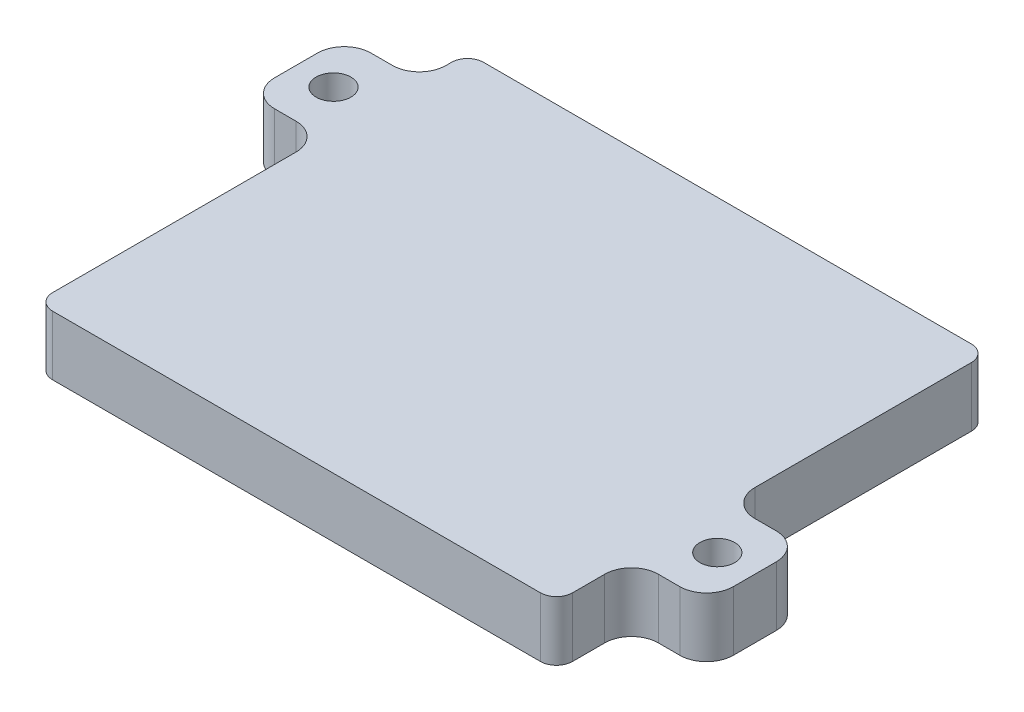
SolidWorks part; units mm, degrees
ref_plane "Front Plane" through (0, 0, 0) normal (0, 0, 1) x (1, 0, 0)
ref_plane "Top Plane" through (0, 0, 0) normal (0, 1, 0) x (1, 0, 0)
ref_plane "Right Plane" through (0, 0, 0) normal (1, 0, 0) x (0, 0, -1)
sketch "Sketch1" plane through (0, 0, 0) normal (0, 1, 0) x (1, 0, 0)
  line L1 (-45.0661, 38.3957) -> (51.9339, 38.3957)
  line L2 (-45.0661, 38.3957) -> (-45.0661, -42.0055)
  line L3 (-45.0661, -42.0055) -> (51.9339, -42.0055)
  line L4 (51.9339, 38.3957) -> (51.9339, -42.0055)
extrude "Boss-Extrude1" add sketch "Sketch1" along normal blind 12.6
sketch "Sketch3" plane through (0, 12.6, 0) normal (0, 1, 0) x (1, 0, 0)
  line L4 (-41.3661, 31.8316) -> (-41.3661, -34.1684)
  line L5 (-39.8661, -35.6684) -> (46.1339, -35.6684)
  line L6 (47.6339, -34.1684) -> (47.6339, 31.8316)
  line L7 (46.1339, 33.3316) -> (-39.8661, 33.3316)
  arc A4 (-41.3661, -34.1684) -> (-39.8661, -35.6684) centre (-39.8661, -34.1684) ccw
  arc A5 (46.1339, -35.6684) -> (47.6339, -34.1684) centre (46.1339, -34.1684) ccw
  arc A6 (47.6339, 31.8316) -> (46.1339, 33.3316) centre (46.1339, 31.8316) ccw
  arc A7 (-39.8661, 33.3316) -> (-41.3661, 31.8316) centre (-39.8661, 31.8316) ccw
extrude "Cut-Extrude2" cut sketch "Sketch3" against normal blind 10 from offset 5 offset against normal yes
sketch "Sketch6" plane through (0, 0, 0) normal (0, -1, 0) x (1, 0, 0)
  line L5 (51.9339, -38.3957) -> (-45.0661, -38.3957)
  line L6 (51.9339, -38.3957) -> (51.9339, 42.0055)
  line L7 (51.9339, 42.0055) -> (-45.0661, 42.0055)
  line L8 (-39.8661, -34.3316) -> (46.1339, -34.3316)
  line L9 (-42.3661, 34.1684) -> (-42.3661, -31.8316)
  line L10 (46.1339, 36.6684) -> (-39.8661, 36.6684)
  line L11 (48.6339, -31.8316) -> (48.6339, 34.1684)
  line L12 (-39.8661, -34.3316) -> (46.1339, -34.3316)
  line L13 (-42.3661, 34.1684) -> (-42.3661, -31.8316)
  line L14 (46.1339, 36.6684) -> (-39.8661, 36.6684)
  line L15 (48.6339, -31.8316) -> (48.6339, 34.1684)
  line L16 (-45.0661, -38.3957) -> (-45.0661, 42.0055)
  arc A8 (-42.3661, -31.8316) -> (-39.8661, -34.3316) centre (-39.8661, -31.8316) ccw
  arc A9 (-39.8661, 36.6684) -> (-42.3661, 34.1684) centre (-39.8661, 34.1684) ccw
  arc A10 (48.6339, 34.1684) -> (46.1339, 36.6684) centre (46.1339, 34.1684) ccw
  arc A11 (46.1339, -34.3316) -> (48.6339, -31.8316) centre (46.1339, -31.8316) ccw
  arc A12 (-42.3661, -31.8316) -> (-39.8661, -34.3316) centre (-39.8661, -31.8316) ccw
  arc A13 (-39.8661, 36.6684) -> (-42.3661, 34.1684) centre (-39.8661, 34.1684) ccw
  arc A14 (48.6339, 34.1684) -> (46.1339, 36.6684) centre (46.1339, 34.1684) ccw
  arc A15 (46.1339, -34.3316) -> (48.6339, -31.8316) centre (46.1339, -31.8316) ccw
  dimension "D1" = 1
extrude "Cut-Extrude3" cut sketch "Sketch6" against normal blind 1.5
fillet "Fillet1" radius 3 4 edges at (51.9339, 7.05, -38.3957) (-45.0661, 7.05, -38.3957) (-45.0661, 7.05, 42.0055) (51.9339, 7.05, 42.0055)
sketch "Sketch7" plane through (-45.0661, 0, 0) normal (-1, 0, 0) x (0, 0, 1)
  line L0 (-35.3957, 12.6) -> (39.0055, 12.6) construction
  line L2 (39.0055, 1.5) -> (-35.3957, 1.5) construction
  line L3 (-35.3957, 12.6) -> (-35.3957, 1.5) construction
  line L4 (-29.3957, 12.6) -> (-11.3957, 12.6)
  line L5 (-29.3957, 12.6) -> (-29.3957, 1.5)
  line L6 (-29.3957, 1.5) -> (-11.3957, 1.5)
  line L7 (-11.3957, 12.6) -> (-11.3957, 1.5)
  line L8 (-29.3957, 12.6) -> (-11.3957, 1.5) construction
  line L9 (-29.3957, 1.5) -> (-11.3957, 12.6) construction
  point P6 (-20.3957, 7.05)
  dimension "D1" = 18
  dimension "D2" = 15
sketch "Sketch8" plane through (51.9339, 0, 0) normal (1, 0, 0) x (0, 0, -1)
  line L0 (-39.0055, 12.6) -> (35.3957, 12.6) construction
  line L2 (35.3957, 1.5) -> (-39.0055, 1.5) construction
  line L3 (-39.0055, 12.6) -> (-39.0055, 1.5) construction
  line L4 (-28.0055, 12.6) -> (-10.0055, 12.6)
  line L5 (-28.0055, 12.6) -> (-28.0055, 1.5)
  line L6 (-28.0055, 1.5) -> (-10.0055, 1.5)
  line L7 (-10.0055, 12.6) -> (-10.0055, 1.5)
  line L8 (-28.0055, 12.6) -> (-10.0055, 1.5) construction
  line L9 (-28.0055, 1.5) -> (-10.0055, 12.6) construction
  point P6 (-19.0055, 7.05)
  dimension "D1" = 18
  dimension "D2" = 20
extrude "Boss-Extrude2" add sketch "Sketch7" along normal blind 14
extrude "Boss-Extrude3" add sketch "Sketch8" along normal blind 14
fillet "Fillet2" radius 5 8 edges at (-45.0661, 7.05, -11.3957) (-59.0661, 7.05, -11.3957) (-45.0661, 7.05, -29.3957) (-59.0661, 7.05, -29.3957) (51.9339, 7.05, 28.0055) (51.9339, 7.05, 10.0055) (65.9339, 7.05, 28.0055) (65.9339, 7.05, 10.0055)
sketch "Sketch9" plane through (0, 12.6, 0) normal (0, 1, 0) x (1, 0, 0)
  line L0 (65.9339, -19.0055) -> (-67.2596, -19.0055) construction
  line L1 (65.9339, -15.0055) -> (65.9339, -23.0055) construction
  line L2 (-59.0661, 16.3957) -> (-59.0661, 24.3957) construction
  line L3 (-59.0661, 20.3957) -> (-8.5439, 20.3957) construction
  circle A0 centre (58.9339, -19.0055) radius 3.25
  circle A1 centre (-52.0661, 20.3957) radius 3.25
  dimension "D3" = 6.5
  dimension "D4" = 6.5
  dimension "D1" = 7
  dimension "D2" = 7
extrude "Cut-Extrude4" cut sketch "Sketch9" against normal through all
sketch "Sketch10" plane through (0, 0, 0) normal (0, 1, 0) x (1, 0, 0)
  line L4 (46.1339, 33.3316) -> (-39.8661, 33.3316)
  line L5 (-41.3661, 31.8316) -> (-41.3661, -34.1684)
  line L6 (-39.8661, -35.6684) -> (46.1339, -35.6684)
  line L7 (47.6339, -34.1684) -> (47.6339, 31.8316)
  line L8 (46.1339, 33.3316) -> (-39.8661, 33.3316)
  line L9 (-41.3661, 31.8316) -> (-41.3661, -34.1684)
  line L10 (-39.8661, -35.6684) -> (46.1339, -35.6684)
  line L11 (47.6339, -34.1684) -> (47.6339, 31.8316)
  line L12 (-59.0661, 24.3957) -> (-59.0661, 16.3957)
  line L13 (-54.0661, 11.3957) -> (-50.0661, 11.3957)
  line L14 (-45.0661, 6.3957) -> (-45.0661, -39.0055)
  line L15 (-42.0661, -42.0055) -> (48.9339, -42.0055)
  line L16 (51.9339, -39.0055) -> (51.9339, -33.0055)
  line L17 (56.9339, -28.0055) -> (60.9339, -28.0055)
  line L18 (65.9339, -23.0055) -> (65.9339, -15.0055)
  line L19 (60.9339, -10.0055) -> (56.9339, -10.0055)
  line L20 (51.9339, -5.0055) -> (51.9339, 35.3957)
  line L21 (48.9339, 38.3957) -> (-42.0661, 38.3957)
  line L22 (-45.0661, 35.3957) -> (-45.0661, 34.3957)
  line L23 (-50.0661, 29.3957) -> (-54.0661, 29.3957)
  line L24 (-59.0661, 24.3957) -> (-59.0661, 16.3957)
  line L25 (-54.0661, 11.3957) -> (-50.0661, 11.3957)
  line L26 (-45.0661, 6.3957) -> (-45.0661, -39.0055)
  line L27 (-42.0661, -42.0055) -> (48.9339, -42.0055)
  line L28 (51.9339, -39.0055) -> (51.9339, -33.0055)
  line L29 (56.9339, -28.0055) -> (60.9339, -28.0055)
  line L30 (65.9339, -23.0055) -> (65.9339, -15.0055)
  line L31 (60.9339, -10.0055) -> (56.9339, -10.0055)
  line L32 (51.9339, -5.0055) -> (51.9339, 35.3957)
  line L33 (48.9339, 38.3957) -> (-42.0661, 38.3957)
  line L34 (-45.0661, 35.3957) -> (-45.0661, 34.3957)
  line L35 (-50.0661, 29.3957) -> (-54.0661, 29.3957)
  line L36 (46.1339, 34.3316) -> (-39.8661, 34.3316)
  line L37 (48.6339, -34.1684) -> (48.6339, 31.8316)
  line L38 (-39.8661, -36.6684) -> (46.1339, -36.6684)
  line L39 (-42.3661, 31.8316) -> (-42.3661, -34.1684)
  line L40 (46.1339, 34.3316) -> (-39.8661, 34.3316)
  line L41 (48.6339, -34.1684) -> (48.6339, 31.8316)
  line L42 (-39.8661, -36.6684) -> (46.1339, -36.6684)
  line L43 (-42.3661, 31.8316) -> (-42.3661, -34.1684)
  circle A0 centre (-52.0661, 20.3957) radius 3.25 construction
  circle A1 centre (58.9339, -19.0055) radius 3.25 construction
  circle A2 centre (-52.0661, 20.3957) radius 3.25
  circle A3 centre (58.9339, -19.0055) radius 3.25
  arc A8 (-39.8661, 33.3316) -> (-41.3661, 31.8316) centre (-39.8661, 31.8316) ccw
  arc A9 (-41.3661, -34.1684) -> (-39.8661, -35.6684) centre (-39.8661, -34.1684) ccw
  arc A10 (46.1339, -35.6684) -> (47.6339, -34.1684) centre (46.1339, -34.1684) ccw
  arc A11 (47.6339, 31.8316) -> (46.1339, 33.3316) centre (46.1339, 31.8316) ccw
  arc A12 (-59.0661, 16.3957) -> (-54.0661, 11.3957) centre (-54.0661, 16.3957) ccw
  arc A13 (-45.0661, 6.3957) -> (-50.0661, 11.3957) centre (-50.0661, 6.3957) ccw
  arc A14 (-45.0661, -39.0055) -> (-42.0661, -42.0055) centre (-42.0661, -39.0055) ccw
  arc A15 (48.9339, -42.0055) -> (51.9339, -39.0055) centre (48.9339, -39.0055) ccw
  arc A16 (56.9339, -28.0055) -> (51.9339, -33.0055) centre (56.9339, -33.0055) ccw
  arc A17 (60.9339, -28.0055) -> (65.9339, -23.0055) centre (60.9339, -23.0055) ccw
  arc A18 (65.9339, -15.0055) -> (60.9339, -10.0055) centre (60.9339, -15.0055) ccw
  arc A19 (51.9339, -5.0055) -> (56.9339, -10.0055) centre (56.9339, -5.0055) ccw
  arc A20 (51.9339, 35.3957) -> (48.9339, 38.3957) centre (48.9339, 35.3957) ccw
  arc A21 (-42.0661, 38.3957) -> (-45.0661, 35.3957) centre (-42.0661, 35.3957) ccw
  arc A22 (-50.0661, 29.3957) -> (-45.0661, 34.3957) centre (-50.0661, 34.3957) ccw
  arc A23 (-54.0661, 29.3957) -> (-59.0661, 24.3957) centre (-54.0661, 24.3957) ccw
  arc A24 (-59.0661, 16.3957) -> (-54.0661, 11.3957) centre (-54.0661, 16.3957) ccw
  arc A25 (-45.0661, 6.3957) -> (-50.0661, 11.3957) centre (-50.0661, 6.3957) ccw
  arc A26 (-45.0661, -39.0055) -> (-42.0661, -42.0055) centre (-42.0661, -39.0055) ccw
  arc A27 (48.9339, -42.0055) -> (51.9339, -39.0055) centre (48.9339, -39.0055) ccw
  arc A28 (56.9339, -28.0055) -> (51.9339, -33.0055) centre (56.9339, -33.0055) ccw
  arc A29 (60.9339, -28.0055) -> (65.9339, -23.0055) centre (60.9339, -23.0055) ccw
  arc A30 (65.9339, -15.0055) -> (60.9339, -10.0055) centre (60.9339, -15.0055) ccw
  arc A31 (51.9339, -5.0055) -> (56.9339, -10.0055) centre (56.9339, -5.0055) ccw
  arc A32 (51.9339, 35.3957) -> (48.9339, 38.3957) centre (48.9339, 35.3957) ccw
  arc A33 (-42.0661, 38.3957) -> (-45.0661, 35.3957) centre (-42.0661, 35.3957) ccw
  arc A34 (-50.0661, 29.3957) -> (-45.0661, 34.3957) centre (-50.0661, 34.3957) ccw
  arc A35 (-54.0661, 29.3957) -> (-59.0661, 24.3957) centre (-54.0661, 24.3957) ccw
  arc A36 (-39.8661, 33.3316) -> (-41.3661, 31.8316) centre (-39.8661, 31.8316) ccw
  arc A37 (-41.3661, -34.1684) -> (-39.8661, -35.6684) centre (-39.8661, -34.1684) ccw
  arc A38 (46.1339, -35.6684) -> (47.6339, -34.1684) centre (46.1339, -34.1684) ccw
  arc A39 (47.6339, 31.8316) -> (46.1339, 33.3316) centre (46.1339, 31.8316) ccw
  arc A40 (-39.8661, 34.3316) -> (-42.3661, 31.8316) centre (-39.8661, 31.8316) ccw
  arc A41 (48.6339, 31.8316) -> (46.1339, 34.3316) centre (46.1339, 31.8316) ccw
  arc A42 (46.1339, -36.6684) -> (48.6339, -34.1684) centre (46.1339, -34.1684) ccw
  arc A43 (-42.3661, -34.1684) -> (-39.8661, -36.6684) centre (-39.8661, -34.1684) ccw
  arc A44 (-39.8661, 34.3316) -> (-42.3661, 31.8316) centre (-39.8661, 31.8316) ccw
  arc A45 (48.6339, 31.8316) -> (46.1339, 34.3316) centre (46.1339, 31.8316) ccw
  arc A46 (46.1339, -36.6684) -> (48.6339, -34.1684) centre (46.1339, -34.1684) ccw
  arc A47 (-42.3661, -34.1684) -> (-39.8661, -36.6684) centre (-39.8661, -34.1684) ccw
  dimension "D1" = 0
  dimension "D2" = 0
  dimension "D3" = 0
